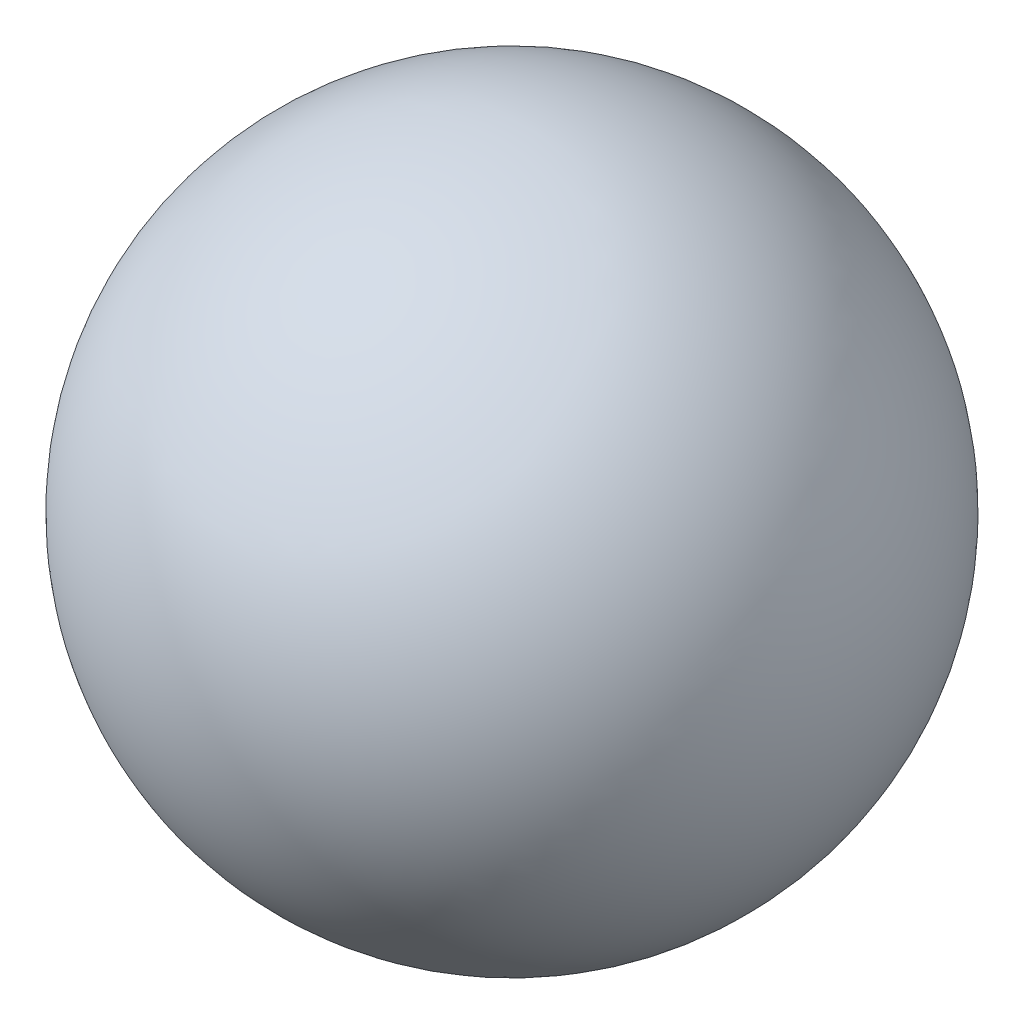
SolidWorks part; units mm, degrees
ref_plane "Front Plane" through (0, 0, 0) normal (0, 0, 1) x (1, 0, 0)
ref_plane "Top Plane" through (0, 0, 0) normal (0, 1, 0) x (1, 0, 0)
ref_plane "Right Plane" through (0, 0, 0) normal (1, 0, 0) x (0, 0, -1)
sketch "Sketch1" plane through (0, 0, 0) normal (0, 1, 0) x (1, 0, 0)
  line L0 (0, 9.525) -> (0, -9.525)
  arc A0 (0, -9.525) -> (0, 9.525) centre (0, 0) ccw
  dimension "D1" = 19.05
revolve "Revolve1" add sketch "Sketch1" angle 360 about L0
